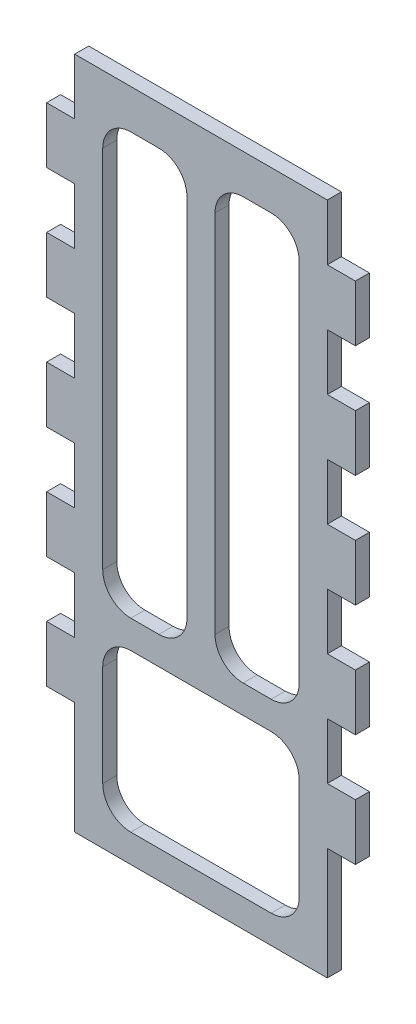
SolidWorks part; units mm, degrees
ref_plane "Front Plane" through (0, 0, 0) normal (0, 0, 1) x (1, 0, 0)
ref_plane "Top Plane" through (0, 0, 0) normal (0, 1, 0) x (1, 0, 0)
ref_plane "Right Plane" through (0, 0, 0) normal (1, 0, 0) x (0, 0, -1)
sketch "Sketch1" plane through (0, 0, 0) normal (0, 0, 1) x (1, 0, 0)
  line L1 (0, 0) -> (57.15, 0)
  line L2 (0, 0) -> (0, 152.4)
  line L3 (0, 152.4) -> (57.15, 152.4)
  line L4 (57.15, 0) -> (57.15, 152.4)
  dimension "D1" = 57.15
  dimension "D2" = 152.4
extrude "Boss-Extrude1" add sketch "Sketch1" along normal blind 3.175
sketch "Sketch2" plane through (0, 0, 3.175) normal (0, 0, 1) x (1, 0, 0)
  line L0 (0, 152.4) -> (0, 0) construction
  line L1 (0, 139.7) -> (-6.35, 139.7)
  line L2 (0, 139.7) -> (0, 127)
  line L3 (0, 127) -> (-6.35, 127)
  line L4 (-6.35, 139.7) -> (-6.35, 127)
  line L5 (57.15, 0) -> (57.15, 152.4) construction
  line L6 (57.15, 139.7) -> (63.5, 139.7)
  line L7 (57.15, 139.7) -> (57.15, 127)
  line L8 (57.15, 127) -> (63.5, 127)
  line L9 (63.5, 139.7) -> (63.5, 127)
  line L10 (57.15, 152.4) -> (0, 152.4) construction
  dimension "D1" = 6.35
  dimension "D2" = 6.35
  dimension "D3" = 12.7
  dimension "D4" = 12.7
  dimension "D5" = 12.7
  dimension "D6" = 12.7
extrude "Boss-Extrude2" add sketch "Sketch2" against normal blind 3.175
pattern_linear "LPattern1" count 5 spacing 25.4 along (0, -1, 0) of "Boss-Extrude2"
sketch "Sketch3" plane through (0, 0, 3.175) normal (0, 0, 1) x (1, 0, 0)
  line L0 (0, 0) -> (57.15, 0) construction
  line L1 (6.35, 41.91) -> (50.8, 41.91)
  line L2 (6.35, 41.91) -> (6.35, 6.35)
  line L3 (6.35, 6.35) -> (50.8, 6.35)
  line L4 (50.8, 41.91) -> (50.8, 6.35)
  line L5 (0, 25.4) -> (0, 0) construction
  line L6 (57.15, 0) -> (57.15, 25.4) construction
  dimension "D1" = 35.56
  dimension "D2" = 6.35
  dimension "D3" = 6.35
  dimension "D4" = 6.35
extrude "Cut-Extrude1" cut sketch "Sketch3" against normal blind 3.175
sketch "Sketch4" plane through (0, 0, 3.175) normal (0, 0, 1) x (1, 0, 0)
  line L0 (0, 152.4) -> (0, 139.7) construction
  line L1 (6.35, 143.51) -> (25.4, 143.51)
  line L2 (6.35, 143.51) -> (6.35, 48.26)
  line L3 (6.35, 48.26) -> (25.4, 48.26)
  line L4 (25.4, 143.51) -> (25.4, 48.26)
  line L5 (31.75, 143.51) -> (50.8, 143.51)
  line L6 (31.75, 143.51) -> (31.75, 48.26)
  line L7 (31.75, 48.26) -> (50.8, 48.26)
  line L8 (50.8, 143.51) -> (50.8, 48.26)
  line L9 (57.15, 114.3) -> (57.15, 127) construction
  line L10 (50.8, 41.91) -> (6.35, 41.91) construction
  dimension "D1" = 95.25
  dimension "D2" = 95.25
  dimension "D3" = 19.05
  dimension "D4" = 19.05
  dimension "D5" = 6.35
  dimension "D6" = 6.35
  dimension "D7" = 6.35
  dimension "D8" = 0
extrude "Cut-Extrude2" cut sketch "Sketch4" against normal blind 3.175
fillet "Fillet1" radius 6.35 12 edges at (50.8, 41.91, 1.5875) (6.35, 41.91, 1.5875) (50.8, 6.35, 1.5875) (6.35, 6.35, 1.5875) (50.8, 143.51, 1.5875) (25.4, 143.51, 1.5875) (31.75, 143.51, 1.5875) (6.35, 143.51, 1.5875) (31.75, 48.26, 1.5875) (50.8, 48.26, 1.5875) (25.4, 48.26, 1.5875) (6.35, 48.26, 1.5875)
